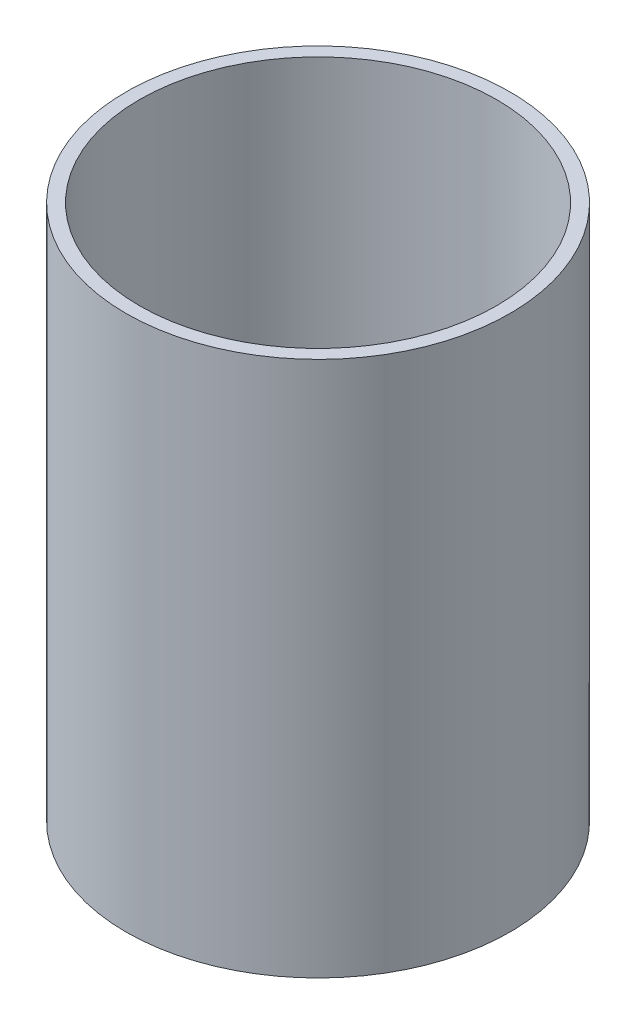
SolidWorks part; units mm, degrees
ref_plane "Front Plane" through (0, 0, 0) normal (0, 0, 1) x (1, 0, 0)
ref_plane "Top Plane" through (0, 0, 0) normal (0, 1, 0) x (1, 0, 0)
ref_plane "Right Plane" through (0, 0, 0) normal (1, 0, 0) x (0, 0, -1)
sketch "Sketch2" plane through (0, 0, 0) normal (0, 1, 0) x (1, 0, 0)
  circle A0 centre (0, 0) radius 25.4
  circle A1 centre (0, 0) radius 27.305
  dimension "D1" = 54.61
  dimension "D2" = 50.8
extrude "Boss-Extrude1" add sketch "Sketch2" along normal blind 76.2
